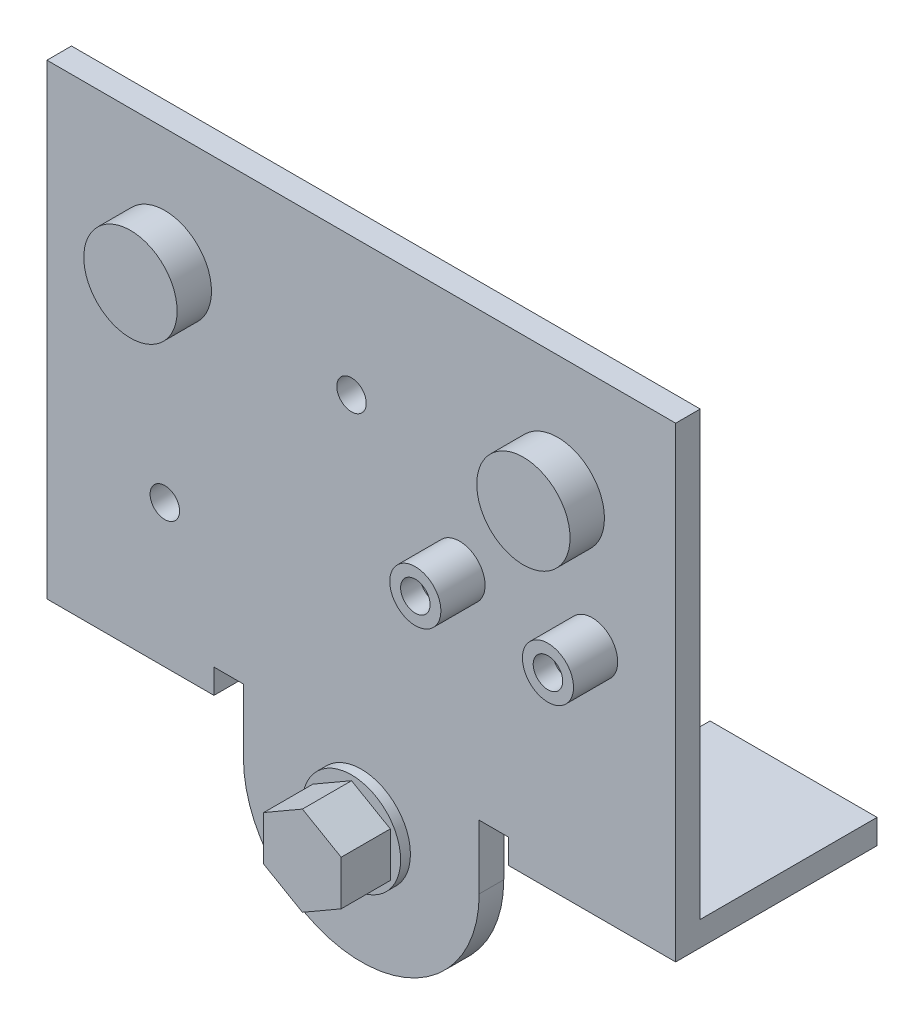
SolidWorks part; units mm, degrees
ref_plane "Front Plane" through (0, 0, 0) normal (0, 0, 1) x (1, 0, 0)
ref_plane "Top Plane" through (0, 0, 0) normal (0, 1, 0) x (1, 0, 0)
ref_plane "Right Plane" through (0, 0, 0) normal (1, 0, 0) x (0, 0, -1)
sketch "Sketch1" plane through (0, 0, 0) normal (0, 0, 1) x (1, 0, 0)
  line L0 (0, -55) -> (0, 55) construction
  line L1 (-32, 19.8519) -> (32, 19.8519)
  line L2 (-32, 19.8519) -> (-32, -25.1481)
  line L3 (-32, -25.1481) -> (32, -25.1481)
  line L4 (32, 19.8519) -> (32, -25.1481)
  dimension "D1" = 64
  dimension "D2" = 45
  dimension "D3" = 32
extrude "Boss-Extrude1" add sketch "Sketch1" along normal blind 2.5
sketch "Sketch3" plane through (0, -25.1481, 0) normal (0, -1, 0) x (1, 0, 0)
  line L0 (-32, 2.5) -> (-32, 0) construction
  line L1 (-32, 2.5) -> (-15, 2.5)
  line L2 (-32, 2.5) -> (-32, -18)
  line L3 (-32, -18) -> (-15, -18)
  line L4 (-15, 2.5) -> (-15, -18)
  line L5 (-32, 2.5) -> (32, 2.5) construction
  line L6 (0, -55) -> (0, 55) construction
  line L7 (32, -18) -> (15, -18)
  line L8 (15, 2.5) -> (15, -18)
  line L9 (32, 2.5) -> (15, 2.5)
  line L10 (32, 2.5) -> (32, -18)
  dimension "D1" = 17
  dimension "D2" = 20.5
extrude "Boss-Extrude2" add sketch "Sketch3" along normal blind 2.5
sketch "Sketch5" plane through (0, 0, 2.5) normal (0, 0, 1) x (1, 0, 0)
  line L0 (-12, -25.1481) -> (-12, -31.6481)
  line L1 (-15, -25.1481) -> (15, -25.1481) construction
  line L2 (12, -25.1481) -> (12, -31.6481)
  line L3 (-32, 19.8519) -> (-32, -27.6481) construction
  line L12 (-32, 19.8519) -> (-32, -27.6481)
  line L13 (-32, -27.6481) -> (-15, -27.6481)
  line L14 (-15, -27.6481) -> (-15, -25.1481)
  line L15 (-15, -25.1481) -> (15, -25.1481)
  line L16 (15, -25.1481) -> (15, -27.6481)
  line L17 (15, -27.6481) -> (32, -27.6481)
  line L18 (32, -27.6481) -> (32, 19.8519)
  line L19 (32, 19.8519) -> (-32, 19.8519)
  line L23 (-12, -25.1481) -> (12, -25.1481)
  arc A0 (12, -31.6481) -> (-12, -31.6481) centre (0, -31.6481) cw
  dimension "D3" = 12
  dimension "D1" = 32
  dimension "D2" = 6.5
  dimension "D4" = 0
extrude "Boss-Extrude4" add sketch "Sketch5" against normal blind 2.5
sketch "Sketch6" plane through (0, 0, 2.5) normal (0, 0, 1) x (1, 0, 0)
  line L0 (-12, -25.1481) -> (-12, -31.6481) construction
  line L1 (12, -25.1481) -> (15, -25.1481) construction
  circle A0 centre (0, -31.6481) radius 5
  dimension "D1" = 12
  dimension "D3" = 10
  dimension "D2" = 6.5
extrude "Boss-Extrude5" add sketch "Sketch6" along normal blind 1
sketch "Sketch7" plane through (0, 0, 3.5) normal (0, 0, 1) x (1, 0, 0)
  line L7 (0.0077, -27.1643) -> (-3.9334, -29.4397)
  line L8 (-3.9334, -29.4397) -> (-3.9334, -33.9904)
  line L9 (-3.9334, -33.9904) -> (0.0077, -36.2658)
  line L10 (0.0077, -27.1643) -> (3.9487, -29.4397)
  line L11 (3.9487, -29.4397) -> (3.9487, -33.9904)
  line L12 (3.9487, -33.9904) -> (0.0077, -36.2658)
  point P2 (0.0065, -31.7156)
  dimension "D1" = 3.94
  dimension "D2" = 4.55
  dimension "D4" = 120
  dimension "D6" = 120
extrude "Boss-Extrude6" add sketch "Sketch7" along normal blind 5
sketch "Sketch8" plane through (0, 0, 2.5) normal (0, 0, 1) x (1, 0, 0)
  line L0 (-32, 19.8519) -> (-32, -27.6481) construction
  line L1 (32, 19.8519) -> (-32, 19.8519) construction
  line L2 (32, -27.6481) -> (32, 19.8519) construction
  circle A0 centre (-20, -13.1481) radius 1.5
  circle A1 centre (-1, 5.8519) radius 1.5
  dimension "D1" = 3
  dimension "D2" = 3
  dimension "D3" = 12
  dimension "D4" = 33
  dimension "D5" = 33
  dimension "D6" = 14
extrude "Cut-Extrude1" cut sketch "Sketch8" against normal blind 2.5
sketch "Sketch9" plane through (0, 0, 2.5) normal (0, 0, 1) x (1, 0, 0)
  line L0 (-32, 19.8519) -> (-32, -27.6481) construction
  line L1 (32, 19.8519) -> (-32, 19.8519) construction
  line L2 (32, -27.6481) -> (32, 19.8519) construction
  circle A0 centre (-20, 7.8519) radius 4.75
  circle A1 centre (20, 7.8519) radius 4.75
  dimension "D5" = 9.5
  dimension "D6" = 9.5
  dimension "D1" = 12
  dimension "D2" = 12
  dimension "D3" = 12
  dimension "D4" = 12
extrude "Boss-Extrude7" add sketch "Sketch9" along normal blind 3.5
sketch "Sketch10" plane through (0, 0, 2.5) normal (0, 0, 1) x (1, 0, 0)
  line L0 (32, -27.6481) -> (32, 19.8519) construction
  line L1 (32, 19.8519) -> (-32, 19.8519) construction
  circle A0 centre (10, -4.1481) radius 2.6
  circle A1 centre (23.5, -4.1481) radius 2.6
  dimension "D1" = 5.2
  dimension "D2" = 5.2
  dimension "D3" = 8.5
  dimension "D4" = 24
  dimension "D5" = 13.5
  dimension "D6" = 24
extrude "Boss-Extrude8" add sketch "Sketch10" along normal blind 4.5
sketch "Sketch11" plane through (0, 0, 7) normal (0, 0, 1) x (1, 0, 0)
  circle A0 centre (10, -4.1481) radius 1.5
  circle A1 centre (10, -4.1481) radius 2.6 construction
  dimension "D1" = 3
  dimension "D2" = 1.1
extrude "Cut-Extrude2" cut sketch "Sketch11" against normal blind 2
sketch "Sketch12" plane through (0, 0, 7) normal (0, 0, 1) x (1, 0, 0)
  circle A0 centre (23.5, -4.1481) radius 1.5
  circle A1 centre (23.5, -4.1481) radius 2.6 construction
  dimension "D1" = 3
  dimension "D2" = 0
extrude "Cut-Extrude3" cut sketch "Sketch12" against normal blind 2
